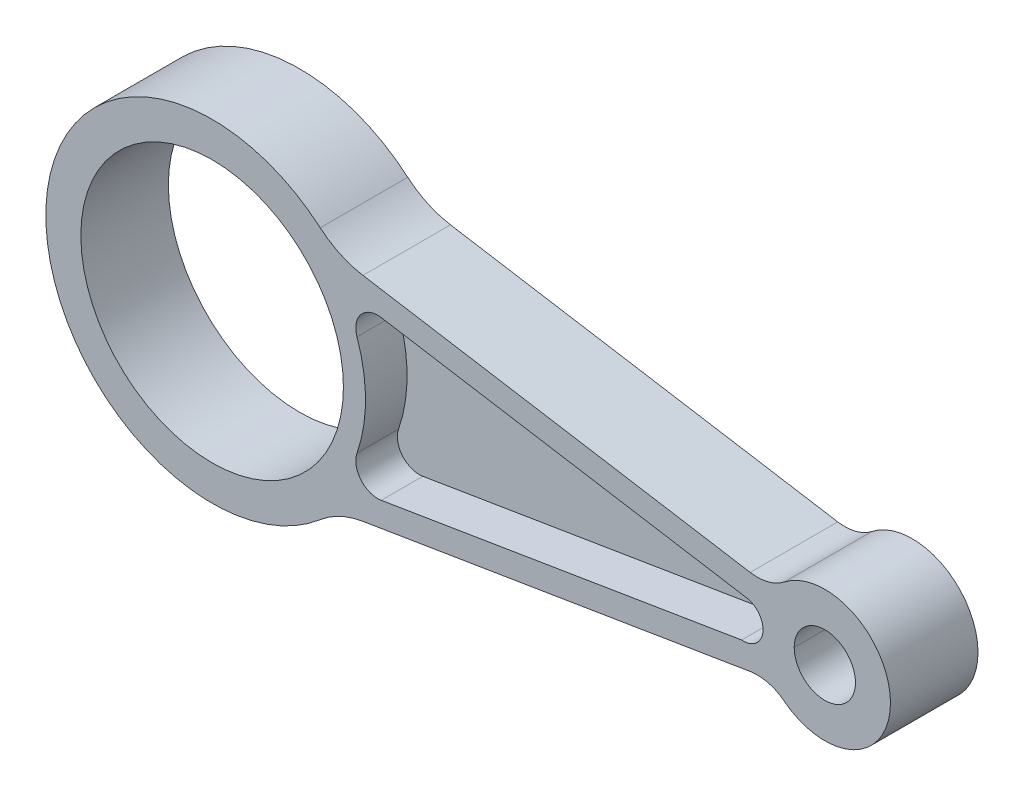
SolidWorks part; units mm, degrees
material "Plain Carbon Steel"
ref_plane "Front Plane" through (0, 0, 0) normal (0, 0, 1) x (1, 0, 0)
ref_plane "Top Plane" through (0, 0, 0) normal (0, 1, 0) x (1, 0, 0)
ref_plane "Right Plane" through (0, 0, 0) normal (1, 0, 0) x (0, 0, -1)
sketch "Sketch1" plane through (0, 0, 0) normal (0, 0, 1) x (1, 0, 0)
  line L0 (-80.1596, 0) -> (125, 0) construction
  line L1 (28.3093, -25.3492) -> (127.981, -8.9746)
  line L3 (133, 0) -> (277.1, 0) construction
  line L4 (28.3093, 25.3492) -> (127.981, 8.9746)
  circle A0 centre (0, 0) radius 30
  arc A1 (28.3093, 25.3492) -> (28.3093, -25.3492) centre (0, 0) ccw
  circle A2 centre (140, 0) radius 7
  arc A3 (127.981, -8.9746) -> (127.981, 8.9746) centre (140, 0) ccw
  dimension "D1" = 60
  dimension "D2" = 76
  dimension "D3" = 14
  dimension "D4" = 30
  dimension "D5" = 140
  dimension "D7" = 6.9074
  dimension "D6" = 99.6716
extrude "Boss-Extrude1" add sketch "Sketch1" along normal mid plane 20
fillet "Fillet1" radius 20 2 edges at (28.3093, -25.3492, 0) (28.3093, 25.3492, 0)
fillet "Fillet2" radius 10 2 edges at (127.981, -8.9746, 0) (127.981, 8.9746, 0)
sketch "Sketch2" plane through (0, 0, 10) normal (0, 0, 1) x (1, 0, 0)
  line L0 (38.6387, 18.0785) -> (121.8484, 4.4083)
  line L1 (38.6387, -18.0785) -> (120.9866, -4.5499)
  line L2 (34.4601, -24.3387) -> (122.9476, -9.8015) construction
  line L3 (122.9476, 9.8015) -> (34.4601, 24.3387) construction
  arc A0 (33.1051, -11.5035) -> (33.1051, 11.5035) centre (0, 0) ccw
  arc A1 (120.9866, -4.5499) -> (121.8484, 4.4083) centre (121.3749, -0.0667) ccw
  arc A2 (33.1051, -11.5035) -> (38.6387, -18.0785) centre (37.8281, -13.1446) ccw
  arc A3 (33.1051, 11.5035) -> (38.6387, 18.0785) centre (37.8281, 13.1446) cw
  point P7 (79.8126, -11.3142)
  dimension "D3" = 4.5
  dimension "D4" = 5
  dimension "D1" = 5.5
  dimension "D2" = 5.5
extrude "Cut-Extrude1" cut sketch "Sketch2" against normal blind 9.5
mirror "Mirror1" about plane through (0, 0, 0) normal (0, 0, 1) of "Cut-Extrude1"
split line "Split Line1"
